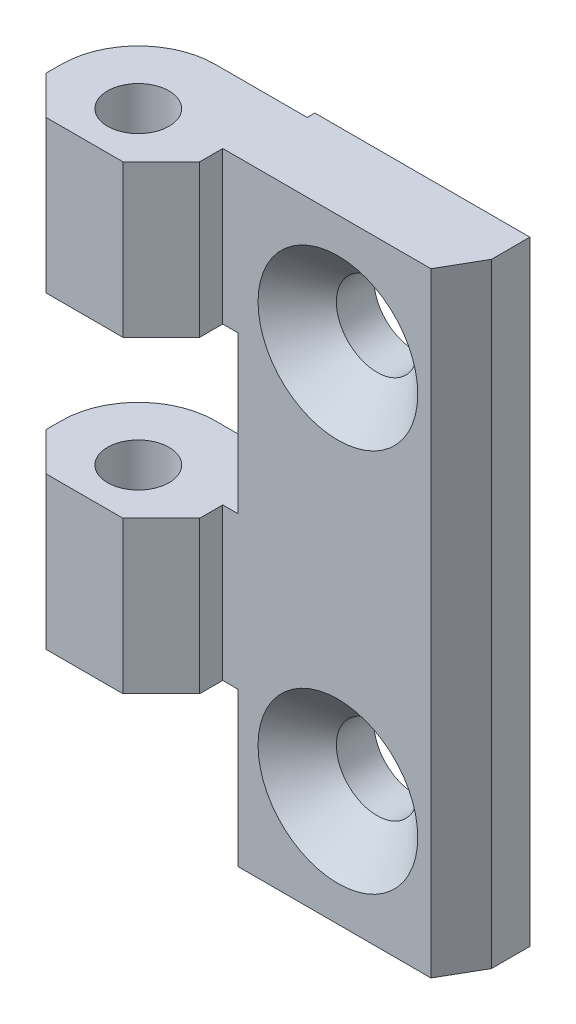
SolidWorks part; units mm, degrees
material "AISI 1035 Steel (SS)"
ref_plane "Front Plane" through (0, 0, 0) normal (0, 0, 1) x (1, 0, 0)
ref_plane "Top Plane" through (0, 0, 0) normal (0, 1, 0) x (1, 0, 0)
ref_plane "Right Plane" through (0, 0, 0) normal (1, 0, 0) x (0, 0, -1)
sketch "Sketch2" plane through (0, 0, 0) normal (0, 1, 0) x (1, 0, 0)
  line L0 (-2.5, 0) -> (2.5, 0)
  line L1 (2.5, 0) -> (5, 2.5)
  line L2 (-2.5, 0) -> (-5, 2.5)
  line L3 (5, 2.5) -> (5, 4)
  line L4 (-5, 2.5) -> (-5, 3.5)
  line L5 (-5, 3.5) -> (0, 3.5) construction
  line L6 (0, 3.5) -> (0, 8.5) construction
  line L7 (0, 8.5) -> (6, 8.5)
  line L8 (6, 8.5) -> (6, 9)
  line L9 (6, 9) -> (20, 9)
  line L10 (5, 4) -> (20, 4)
  line L11 (20, 9) -> (20, 4)
  arc A0 (-5, 3.5) -> (0, 8.5) centre (0, 3.5) cw
  dimension "D1" = 5
  dimension "D2" = 2.5
  dimension "D3" = 2.5
  dimension "D4" = 2.5
  dimension "D5" = 2.5
  dimension "D6" = 1
  dimension "D7" = 1.5
  dimension "D8" = 5
  dimension "D9" = 6
  dimension "D10" = 0.5
  dimension "D11" = 14
extrude "Boss-Extrude1" add sketch "Sketch2" along normal blind 40
sketch "Sketch3" plane through (0, 40, 0) normal (0, 1, 0) x (1, 0, 0)
  line L0 (5, 4) -> (18.56, 4) construction
  line L1 (5, 4) -> (20, 4) construction
  line L2 (20, 9) -> (20, 6.5) construction
  line L3 (20, 4) -> (20, 9) construction
  line L4 (20, 6.5) -> (18.56, 4)
  line L5 (18.56, 4) -> (20, 4)
  line L6 (20, 4) -> (20, 6.5)
  dimension "D1" = 13.56
  dimension "D2" = 2.5
extrude "Cut-Extrude1" cut sketch "Sketch3" against normal up to vertex (40 mm away)
sketch "Sketch5" plane through (0, 0, -4) normal (0, 0, 1) x (1, 0, 0)
  line L0 (-2.5, 40) -> (2.5, 40) construction
  line L1 (5, 0) -> (18.56, 0) construction
  circle A0 centre (12.5, 32.5) radius 2.65
  circle A1 centre (12.5, 7.5) radius 2.65
  point P4 (0, 40)
  dimension "D1" = 5.3
  dimension "D2" = 12.5
  dimension "D3" = 12.5
  dimension "D4" = 25
  dimension "D5" = 7.5
hole_wizard "CSK for M5 Flat Head Machine Screw1" positions "3DSketch3" profile "Sketch6" countersink size "M5" standard "ANSI Metric" end condition through all
sketch3d "3DSketch3"
  point P0 (12.5, 32.5, -4)
  point P3 (12.5, 7.5, -4)
sketch "Sketch6" plane through (12.5, 32.5, -4) normal (1, 0, 0) x (0, -1, 0)
  line L0 (0, 0) -> (0, 5)
  line L1 (0, 5) -> (2.65, 5)
  line L2 (2.65, 5) -> (2.65, 2.55)
  line L3 (2.65, 2.55) -> (5.2, 0)
  line L5 (5.2, 0) -> (0, 0)
  line L6 (-2.65, 2.55) -> (-5.2, 0) construction
  line L11 (0, -6.35) -> (0, 107.95) construction
  dimension "Thru Hole Dia." = 5.3
  dimension "Thru Hole Depth" = 5
  dimension "Near C'Sink Dia." = 10.4
  dimension "Near C'Sink Angle" = 90
sketch "Sketch7" plane through (0, 40, 0) normal (0, 1, 0) x (1, 0, 0)
  circle A0 centre (0, 3.5) radius 2
extrude "Cut-Extrude2" cut sketch "Sketch7" against normal up to vertex (40 mm away)
sketch "Sketch8" plane through (0, 0, -4) normal (0, 0, 1) x (1, 0, 0)
  line L0 (5, 40) -> (5, 30.1) construction
  line L1 (5, 40) -> (5, 0) construction
  line L3 (5, 30.1) -> (6, 30.1)
  line L4 (5, 30.1) -> (5, 19.9)
  line L5 (5, 19.9) -> (6, 19.9)
  line L6 (6, 30.1) -> (6, 19.9)
  dimension "D1" = 9.9
  dimension "D2" = 1
  dimension "D3" = 10.2
extrude "Cut-Extrude3" cut sketch "Sketch8" against normal blind 10
sketch "Sketch9" plane through (0, 0, -4) normal (0, 0, 1) x (1, 0, 0)
  line L1 (6, 30.1) -> (-5.7012, 30.1)
  line L2 (6, 30.1) -> (6, 19.9)
  line L3 (6, 19.9) -> (-5.7012, 19.9)
  line L4 (-5.7012, 30.1) -> (-5.7012, 19.9)
extrude "Cut-Extrude4" cut sketch "Sketch9" against normal blind 10 and the other way blind 10
sketch "Sketch10" plane through (0, 0, -4) normal (0, 0, 1) x (1, 0, 0)
  line L1 (5, 0) -> (6, 0)
  line L2 (5, 0) -> (5, 10)
  line L3 (5, 10) -> (6, 10)
  line L4 (6, 0) -> (6, 10)
  dimension "D1" = 1
  dimension "D2" = 10
extrude "Cut-Extrude5" cut sketch "Sketch10" against normal blind 10
sketch "Sketch11" plane through (0, 0, -4) normal (0, 0, 1) x (1, 0, 0)
  line L1 (6, 10) -> (-6.1658, 10)
  line L2 (6, 10) -> (6, -0.8742)
  line L3 (6, -0.8742) -> (-6.1658, -0.8742)
  line L4 (-6.1658, 10) -> (-6.1658, -0.8742)
extrude "Cut-Extrude6" cut sketch "Sketch11" against normal blind 10 and the other way blind 10
